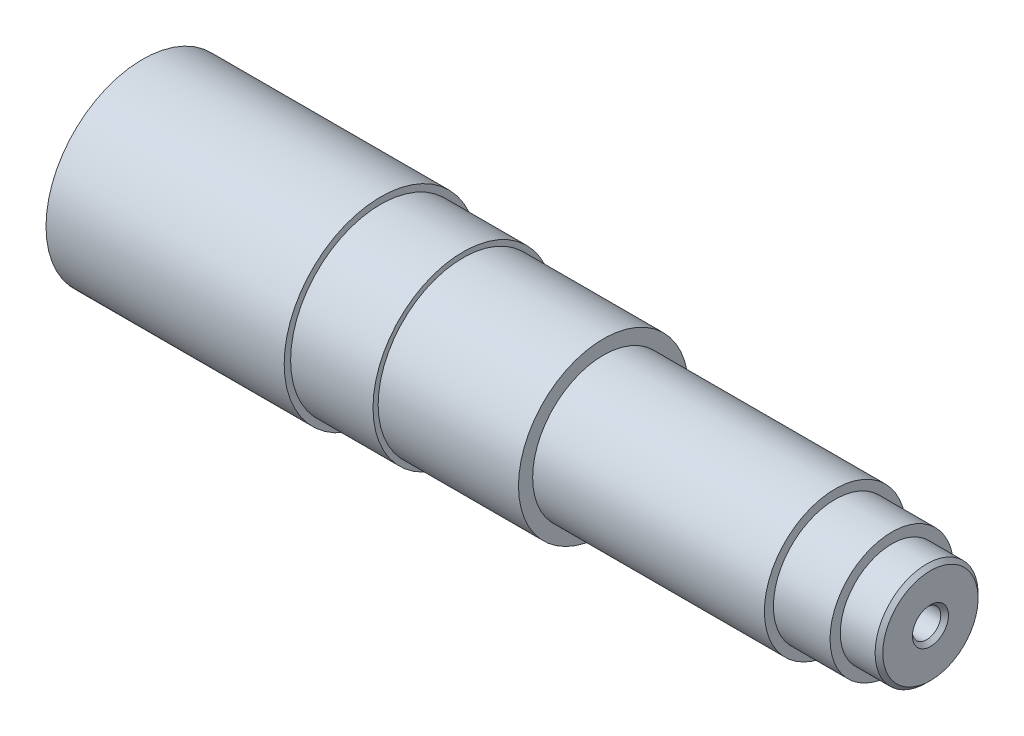
SolidWorks part; units mm, degrees
ref_plane "Front Plane" through (0, 0, 0) normal (0, 0, 1) x (1, 0, 0)
ref_plane "Top Plane" through (0, 0, 0) normal (0, 1, 0) x (1, 0, 0)
ref_plane "Right Plane" through (0, 0, 0) normal (1, 0, 0) x (0, 0, -1)
sketch "Sketch1" plane through (0, 0, 0) normal (0, 0, 1) x (1, 0, 0)
  line L0 (0, 0) -> (323, 0) construction
  line L1 (0, 0) -> (0, 12.2)
  line L2 (2.5, 14.7) -> (17, 14.7)
  line L3 (17, 14.7) -> (17, 37.5)
  line L4 (17, 37.5) -> (109.5, 37.5)
  line L5 (109.5, 37.5) -> (109.5, 35)
  line L6 (109.5, 35) -> (141.5, 35)
  line L7 (141.5, 35) -> (141.5, 33)
  line L8 (141.5, 33) -> (196, 33)
  line L9 (196, 33) -> (196, 27.5)
  line L10 (196, 27.5) -> (286, 27.5)
  line L11 (286, 27.5) -> (286, 24)
  line L12 (286, 24) -> (308, 24)
  line L13 (308, 24) -> (308, 20)
  line L14 (308, 20) -> (321.5, 20)
  line L15 (323, 18.5) -> (323, 0)
  line L16 (321.5, 20) -> (323, 18.5)
  line L17 (0, 12.2) -> (2.5, 14.7)
  line L18 (0, 0) -> (323, 0)
  point P4 (0, 14.7)
  point P17 (323, 20)
  dimension "D1" = 323
  dimension "D2" = 14.7
  dimension "D3" = 17
  dimension "D4" = 37.5
  dimension "D5" = 92.5
  dimension "D6" = 35
  dimension "D7" = 33
  dimension "D8" = 32
  dimension "D9" = 54.5
  dimension "D10" = 90
  dimension "D11" = 27.5
  dimension "D12" = 24
  dimension "D13" = 20
  dimension "D14" = 22
  dimension "D15" = 15
revolve "Revolve1" add sketch "Sketch1" angle 360 about L0
hole_wizard "CSK for M10 Countersunk Flat Head Screw1" positions "Sketch2" profile "Sketch3" countersink size "M10" standard "ISO"
sketch "Sketch2" plane through (0, 0, 0) normal (-1, 0, 0) x (0, 0, 1)
  point P0 (0, 0)
sketch "Sketch3" plane through (0, 0, 0) normal (0, 1, 0) x (0, 0, 1)
  line L0 (0, 0) -> (0, 14)
  line L1 (0, 14) -> (5.5, 10.6953)
  line L2 (5.5, 10.6953) -> (5.5, 1.5)
  line L3 (5.5, 1.5) -> (7, 0)
  line L5 (7, 0) -> (0, 0)
  line L6 (-5.5, 1.5) -> (-7, 0) construction
  line L10 (0, 14) -> (-5.5, 10.6953) construction
  line L11 (0, -6.35) -> (0, 107.95) construction
  dimension "Hole Dia." = 11
  dimension "Hole Depth" = 14
  dimension "Near C'Sink Dia." = 14
  dimension "Near C'Sink Angle" = 90
  dimension "Drill Angle" = 118
hole_wizard "CSK for M10 Countersunk Flat Head Screw2" positions "Sketch4" profile "Sketch5" countersink size "M10" standard "ISO"
sketch "Sketch4" plane through (323, 0, 0) normal (1, 0, 0) x (0, 0, -1)
  point P0 (0, 0)
sketch "Sketch5" plane through (323, 0, 0) normal (0, 1, 0) x (0, 0, -1)
  line L0 (0, 0) -> (0, 14)
  line L1 (0, 14) -> (5.5, 10.6953)
  line L2 (5.5, 10.6953) -> (5.5, 1.5)
  line L3 (5.5, 1.5) -> (7, 0)
  line L5 (7, 0) -> (0, 0)
  line L6 (-5.5, 1.5) -> (-7, 0) construction
  line L10 (0, 14) -> (-5.5, 10.6953) construction
  line L11 (0, -6.35) -> (0, 107.95) construction
  dimension "Hole Dia." = 11
  dimension "Hole Depth" = 14
  dimension "Near C'Sink Dia." = 14
  dimension "Near C'Sink Angle" = 90
  dimension "Drill Angle" = 118
